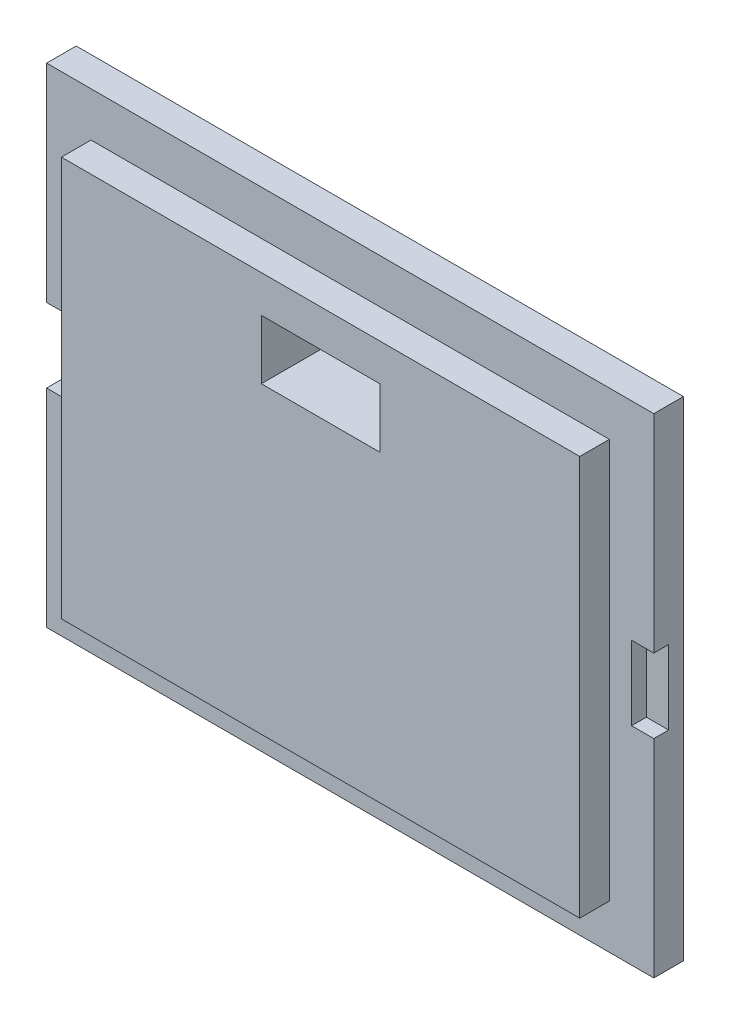
SolidWorks part; units mm, degrees
ref_plane "Спереди" through (0, 0, 0) normal (0, 0, 1) x (1, 0, 0)
ref_plane "Сверху" through (0, 0, 0) normal (0, 1, 0) x (1, 0, 0)
ref_plane "Справа" through (0, 0, 0) normal (1, 0, 0) x (0, 0, -1)
sketch "Эскиз1" plane through (0, 0, 0) normal (0, 0, 1) x (1, 0, 0)
  line L0 (0, 28.3571) -> (0, -25.2143) construction
  line L1 (-34.6429, 0) -> (36.5, 0) construction
  line L3 (-20.5, 16.5) -> (20.5, 16.5)
  line L4 (-20.5, 16.5) -> (-20.5, -16.5)
  line L5 (-20.5, -16.5) -> (20.5, -16.5)
  line L6 (20.5, 16.5) -> (20.5, -16.5)
  point P9 (0, 16.5)
  point P10 (20.5, 0)
  dimension "D1" = 41
  dimension "D2" = 33
extrude "Бобышка-Вытянуть1" add sketch "Эскиз1" along normal blind 2
sketch "Эскиз2" plane through (0, 0, 2) normal (0, 0, 1) x (1, 0, 0)
  line L0 (0, 20) -> (0, -20) construction
  line L1 (-20, 0) -> (20, 0) construction
  line L3 (-17.5, 13.5) -> (17.5, 13.5)
  line L4 (-17.5, 13.5) -> (-17.5, -13.5)
  line L5 (-17.5, -13.5) -> (17.5, -13.5)
  line L6 (17.5, 13.5) -> (17.5, -13.5)
  point P5 (-17.5, 0)
  point P6 (0, 13.5)
  dimension "D1" = 35
  dimension "D2" = 27
extrude "Бобышка-Вытянуть2" add sketch "Эскиз2" along normal blind 2
sketch "Эскиз3" plane through (0, 0, 4) normal (0, 0, 1) x (1, 0, 0)
  line L0 (0, -10.6756) -> (0, 16.0688) construction
  line L1 (-4, 7) -> (4, 7)
  line L2 (-4, 7) -> (-4, 11)
  line L3 (-4, 11) -> (4, 11)
  line L4 (4, 7) -> (4, 11)
  line L5 (-4, 7) -> (4, 11) construction
  line L6 (-4, 11) -> (4, 7) construction
  point P0 (0, 9)
  point P8 (0, 0)
  dimension "D1" = 4
  dimension "D2" = 8
  dimension "D3" = 7
extrude "Вырез-Вытянуть1" cut sketch "Эскиз3" against normal blind 5
sketch "Эскиз5" plane through (0, 0, 2) normal (0, 0, 1) x (1, 0, 0)
  line L0 (-20.5, 16.5) -> (-20.5, -16.5) construction
  line L1 (-20.5, 2.5) -> (-19, 2.5)
  line L2 (-20.5, 2.5) -> (-20.5, -2.5)
  line L3 (-20.5, -2.5) -> (-19, -2.5)
  line L4 (-19, 2.5) -> (-19, -2.5)
  line L5 (0, -8.6968) -> (0, 15.9696) construction
  line L6 (-26.5655, 0) -> (30.2211, 0) construction
  line L7 (20.5, -2.5) -> (19, -2.5)
  line L8 (19, 2.5) -> (19, -2.5)
  line L9 (20.5, 2.5) -> (19, 2.5)
  line L10 (20.5, 2.5) -> (20.5, -2.5)
  point P11 (-19, 0)
  dimension "D1" = 5
  dimension "D2" = 1.5
extrude "Вырез-Вытянуть2" cut sketch "Эскиз5" against normal blind 1
